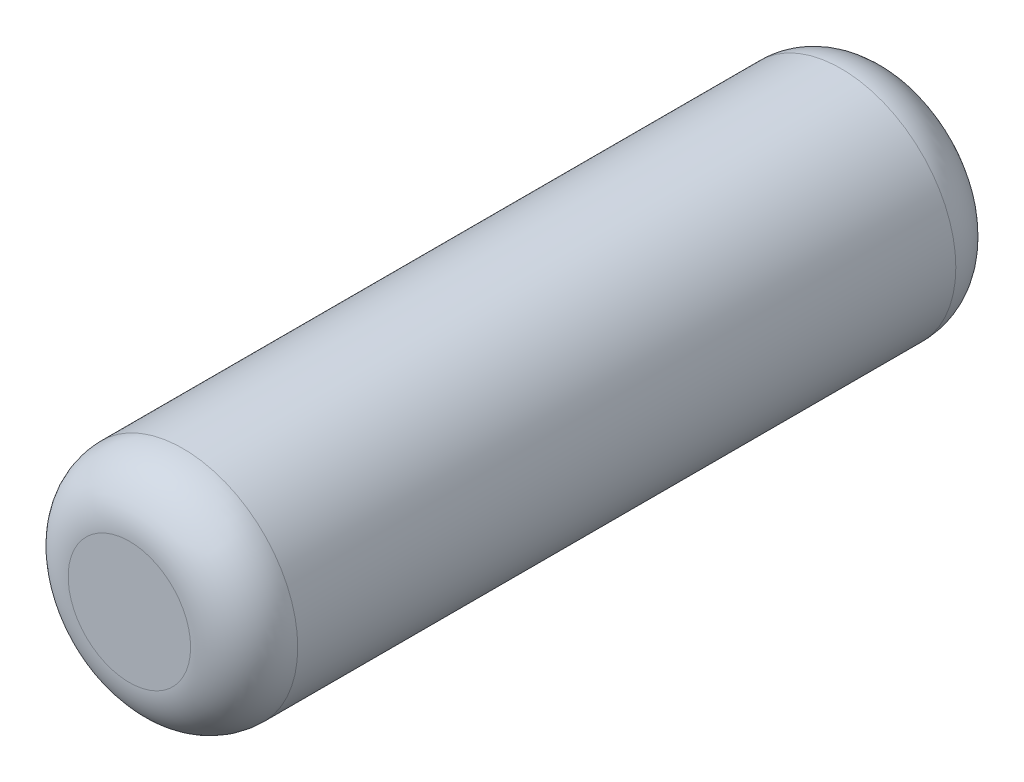
SolidWorks part; units mm, degrees
ref_plane "Front" through (0, 0, 0) normal (0, 0, 1) x (1, 0, 0)
ref_plane "Top" through (0, 0, 0) normal (0, 1, 0) x (1, 0, 0)
ref_plane "Right" through (0, 0, 0) normal (1, 0, 0) x (0, 0, -1)
sketch "Sketch1" plane through (0, 0, 0) normal (0, 0, 1) x (1, 0, 0)
  circle A0 centre (0, 0) radius 0.75
  dimension "D1" = 1.5
extrude "Boss-Extrude1" add sketch "Sketch1" along normal mid plane 5
fillet "Fillet1" radius 0.35 2 edges at (0.75, 0, -2.5) (0.75, 0, 2.5)
